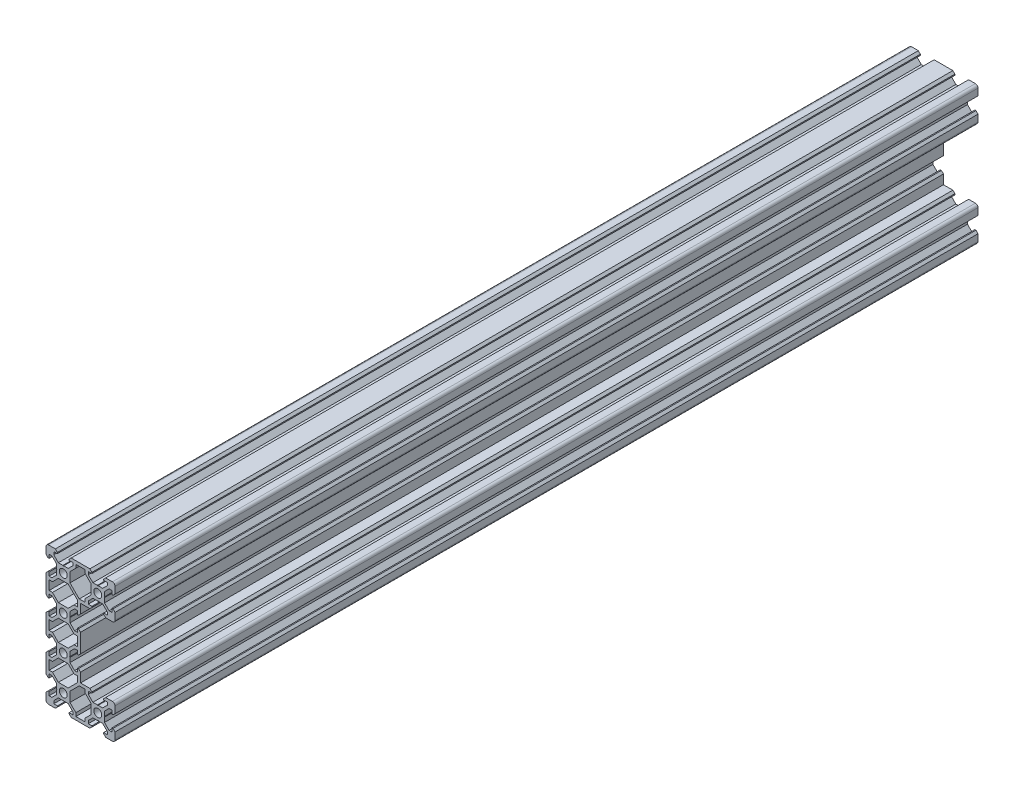
SolidWorks part; units mm, degrees
ref_plane "Front Plane" through (0, 0, 0) normal (0, 0, 1) x (1, 0, 0)
ref_plane "Top Plane" through (0, 0, 0) normal (0, 1, 0) x (1, 0, 0)
ref_plane "Right Plane" through (0, 0, 0) normal (1, 0, 0) x (0, 0, -1)
sketch "Sketch1" plane through (0, 0, 0) normal (0, 0, 1) x (1, 0, 0)
  line B0 (0, -5.42) -> (0, 5.42)
  line B1 (17.3, 38.2) -> (17.3, 36.2393)
  line B2 (17.3, 36.2393) -> (13.9, 32.8393)
  line B3 (13.9, 32.8393) -> (13.9, 27.1607)
  line B4 (19.2607, 21.8) -> (13.9, 27.1607)
  line B5 (22.7, 21.8) -> (19.2607, 21.8)
  line B6 (22.7, 21.8) -> (22.7, 23.7607)
  line B7 (22.7, 23.7607) -> (26.1, 27.1607)
  line B8 (26.1, 32.8393) -> (26.1, 27.1607)
  line B9 (22.7, 36.2393) -> (26.1, 32.8393)
  line B10 (22.7, 38.2) -> (22.7, 36.2393)
  line B11 (17.3, 38.2) -> (22.7, 38.2)
  line B12 (1.8, -22.7) -> (3.7607, -22.7)
  line B13 (3.7607, -22.7) -> (7.1607, -26.1)
  line B14 (7.1607, -26.1) -> (12.8393, -26.1)
  line B15 (18.2, -20.7393) -> (12.8393, -26.1)
  line B16 (18.2, -17.3) -> (18.2, -20.7393)
  line B17 (18.2, -17.3) -> (16.2393, -17.3)
  line B18 (16.2393, -17.3) -> (12.8393, -13.9)
  line B19 (7.1607, -13.9) -> (12.8393, -13.9)
  line B20 (3.7607, -17.3) -> (7.1607, -13.9)
  line B21 (1.8, -17.3) -> (3.7607, -17.3)
  line B22 (1.8, -22.7) -> (1.8, -17.3)
  line B23 (22.7, -38.2) -> (22.7, -36.2393)
  line B24 (22.7, -36.2393) -> (26.1, -32.8393)
  line B25 (26.1, -32.8393) -> (26.1, -27.1607)
  line B26 (22.7, -23.7607) -> (26.1, -27.1607)
  line B27 (22.7, -21.8) -> (22.7, -23.7607)
  line B28 (22.7, -21.8) -> (19.2607, -21.8)
  line B29 (13.9, -27.1607) -> (19.2607, -21.8)
  line B30 (13.9, -32.8393) -> (13.9, -27.1607)
  line B31 (17.3, -36.2393) -> (13.9, -32.8393)
  line B32 (17.3, -38.2) -> (17.3, -36.2393)
  line B33 (22.7, -38.2) -> (17.3, -38.2)
  line B34 (1.8, 17.3) -> (3.7607, 17.3)
  line B35 (3.7607, 17.3) -> (7.1607, 13.9)
  line B36 (7.1607, 13.9) -> (12.8393, 13.9)
  line B37 (16.2393, 17.3) -> (12.8393, 13.9)
  line B38 (18.2, 17.3) -> (16.2393, 17.3)
  line B39 (18.2, 17.3) -> (18.2, 20.7393)
  line B40 (12.8393, 26.1) -> (18.2, 20.7393)
  line B41 (7.1607, 26.1) -> (12.8393, 26.1)
  line B42 (3.7607, 22.7) -> (7.1607, 26.1)
  line B43 (1.8, 22.7) -> (3.7607, 22.7)
  line B44 (1.8, 17.3) -> (1.8, 22.7)
  line B45 (1.8, -2.7) -> (3.7607, -2.7)
  line B46 (3.7607, -2.7) -> (7.1607, -6.1)
  line B47 (7.1607, -6.1) -> (12.8393, -6.1)
  line B48 (16.2393, -2.7) -> (12.8393, -6.1)
  line B49 (18.2, -2.7) -> (16.2393, -2.7)
  line B50 (18.2, -2.7) -> (18.2, 2.7)
  line B51 (18.2, 2.7) -> (16.2393, 2.7)
  line B52 (16.2393, 2.7) -> (12.8393, 6.1)
  line B53 (7.1607, 6.1) -> (12.8393, 6.1)
  line B54 (3.7607, 2.7) -> (7.1607, 6.1)
  line B55 (1.8, 2.7) -> (3.7607, 2.7)
  line B56 (1.8, -2.7) -> (1.8, 2.7)
  line B57 (33.69, 30) -> (33.9, 29.79)
  line B58 (33.9, 29.79) -> (33.9, 27.1607)
  line B59 (33.9, 27.1607) -> (36.5607, 24.5)
  line B60 (36.5607, 24.5) -> (38.2, 24.5)
  line B61 (38.2, 24.5) -> (38.2, 26.605)
  line B62 (38.2, 26.605) -> (38.815, 26.605)
  line B63 (38.815, 26.605) -> (40, 25.42)
  line B64 (40, 25.42) -> (40, 21.5)
  arc B65 (38.5, 20) -> (40, 21.5) centre (38.5, 21.5) ccw
  line B66 (38.5, 20) -> (34.58, 20)
  line B67 (33.395, 21.185) -> (34.58, 20)
  line B68 (33.395, 21.8) -> (33.395, 21.185)
  line B69 (35.5, 21.8) -> (33.395, 21.8)
  line B70 (35.5, 23.4393) -> (35.5, 21.8)
  line B71 (32.8393, 26.1) -> (35.5, 23.4393)
  line B72 (30.21, 26.1) -> (32.8393, 26.1)
  line B73 (30, 26.31) -> (30.21, 26.1)
  line B74 (30, 26.31) -> (29.79, 26.1)
  line B75 (29.79, 26.1) -> (27.1607, 26.1)
  line B76 (27.1607, 26.1) -> (24.5, 23.4393)
  line B77 (24.5, 23.4393) -> (24.5, 21.8)
  line B78 (24.5, 21.8) -> (26.605, 21.8)
  line B79 (26.605, 21.8) -> (26.605, 21.185)
  line B80 (26.605, 21.185) -> (25.42, 20)
  line B81 (25.42, 20) -> (20, 20)
  line B82 (20, 20) -> (20, 14.58)
  line B83 (18.815, 13.395) -> (20, 14.58)
  line B84 (18.2, 13.395) -> (18.815, 13.395)
  line B85 (18.2, 15.5) -> (18.2, 13.395)
  line B86 (16.5607, 15.5) -> (18.2, 15.5)
  line B87 (13.9, 12.8393) -> (16.5607, 15.5)
  line B88 (13.9, 10.21) -> (13.9, 12.8393)
  line B89 (13.69, 10) -> (13.9, 10.21)
  line B90 (13.69, 10) -> (13.9, 9.79)
  line B91 (13.9, 9.79) -> (13.9, 7.1607)
  line B92 (13.9, 7.1607) -> (16.5607, 4.5)
  line B93 (16.5607, 4.5) -> (18.2, 4.5)
  line B94 (18.2, 4.5) -> (18.2, 6.605)
  line B95 (18.2, 6.605) -> (18.815, 6.605)
  line B96 (18.815, 6.605) -> (20, 5.42)
  line B97 (20, 5.42) -> (20, -5.42)
  line B98 (18.815, -6.605) -> (20, -5.42)
  line B99 (18.2, -6.605) -> (18.815, -6.605)
  line B100 (18.2, -4.5) -> (18.2, -6.605)
  line B101 (16.5607, -4.5) -> (18.2, -4.5)
  line B102 (13.9, -7.1607) -> (16.5607, -4.5)
  line B103 (13.9, -9.79) -> (13.9, -7.1607)
  line B104 (13.69, -10) -> (13.9, -9.79)
  line B105 (13.69, -10) -> (13.9, -10.21)
  line B106 (13.9, -10.21) -> (13.9, -12.8393)
  line B107 (13.9, -12.8393) -> (16.5607, -15.5)
  line B108 (16.5607, -15.5) -> (18.2, -15.5)
  line B109 (18.2, -15.5) -> (18.2, -13.395)
  line B110 (18.2, -13.395) -> (18.815, -13.395)
  line B111 (18.815, -13.395) -> (20, -14.58)
  line B112 (20, -14.58) -> (20, -20)
  line B113 (25.42, -20) -> (20, -20)
  line B114 (26.605, -21.185) -> (25.42, -20)
  line B115 (26.605, -21.8) -> (26.605, -21.185)
  line B116 (24.5, -21.8) -> (26.605, -21.8)
  line B117 (24.5, -23.4393) -> (24.5, -21.8)
  line B118 (27.1607, -26.1) -> (24.5, -23.4393)
  line B119 (29.79, -26.1) -> (27.1607, -26.1)
  line B120 (30, -26.31) -> (29.79, -26.1)
  line B121 (30, -26.31) -> (30.21, -26.1)
  line B122 (30.21, -26.1) -> (32.8393, -26.1)
  line B123 (32.8393, -26.1) -> (35.5, -23.4393)
  line B124 (35.5, -23.4393) -> (35.5, -21.8)
  line B125 (35.5, -21.8) -> (33.395, -21.8)
  line B126 (33.395, -21.8) -> (33.395, -21.185)
  line B127 (33.395, -21.185) -> (34.58, -20)
  line B128 (38.5, -20) -> (34.58, -20)
  arc B129 (40, -21.5) -> (38.5, -20) centre (38.5, -21.5) ccw
  line B130 (40, -25.42) -> (40, -21.5)
  line B131 (38.815, -26.605) -> (40, -25.42)
  line B132 (38.2, -26.605) -> (38.815, -26.605)
  line B133 (38.2, -24.5) -> (38.2, -26.605)
  line B134 (36.5607, -24.5) -> (38.2, -24.5)
  line B135 (33.9, -27.1607) -> (36.5607, -24.5)
  line B136 (33.9, -29.79) -> (33.9, -27.1607)
  line B137 (33.69, -30) -> (33.9, -29.79)
  line B138 (33.69, -30) -> (33.9, -30.21)
  line B139 (33.9, -30.21) -> (33.9, -32.8393)
  line B140 (33.9, -32.8393) -> (36.5607, -35.5)
  line B141 (36.5607, -35.5) -> (38.2, -35.5)
  line B142 (38.2, -35.5) -> (38.2, -33.395)
  line B143 (38.2, -33.395) -> (38.815, -33.395)
  line B144 (38.815, -33.395) -> (40, -34.58)
  line B145 (40, -38.5) -> (40, -34.58)
  arc B146 (38.5, -40) -> (40, -38.5) centre (38.5, -38.5) ccw
  line B147 (34.58, -40) -> (38.5, -40)
  line B148 (33.395, -38.815) -> (34.58, -40)
  line B149 (33.395, -38.2) -> (33.395, -38.815)
  line B150 (35.5, -38.2) -> (33.395, -38.2)
  line B151 (35.5, -36.5607) -> (35.5, -38.2)
  line B152 (32.8393, -33.9) -> (35.5, -36.5607)
  line B153 (30.21, -33.9) -> (32.8393, -33.9)
  line B154 (30, -33.69) -> (30.21, -33.9)
  line B155 (30, -33.69) -> (29.79, -33.9)
  line B156 (29.79, -33.9) -> (27.1607, -33.9)
  line B157 (27.1607, -33.9) -> (24.5, -36.5607)
  line B158 (24.5, -36.5607) -> (24.5, -38.2)
  line B159 (24.5, -38.2) -> (26.605, -38.2)
  line B160 (26.605, -38.2) -> (26.605, -38.815)
  line B161 (26.605, -38.815) -> (25.42, -40)
  line B162 (14.58, -40) -> (25.42, -40)
  line B163 (13.395, -38.815) -> (14.58, -40)
  line B164 (13.395, -38.2) -> (13.395, -38.815)
  line B165 (15.5, -38.2) -> (13.395, -38.2)
  line B166 (15.5, -36.5607) -> (15.5, -38.2)
  line B167 (12.8393, -33.9) -> (15.5, -36.5607)
  line B168 (10.21, -33.9) -> (12.8393, -33.9)
  line B169 (10, -33.69) -> (10.21, -33.9)
  line B170 (10, -33.69) -> (9.79, -33.9)
  line B171 (9.79, -33.9) -> (7.1607, -33.9)
  line B172 (7.1607, -33.9) -> (4.5, -36.5607)
  line B173 (4.5, -36.5607) -> (4.5, -38.2)
  line B174 (4.5, -38.2) -> (6.605, -38.2)
  line B175 (6.605, -38.2) -> (6.605, -38.815)
  line B176 (6.605, -38.815) -> (5.42, -40)
  line B177 (1.5, -40) -> (5.42, -40)
  arc B178 (0, -38.5) -> (1.5, -40) centre (1.5, -38.5) ccw
  line B179 (0, -38.5) -> (0, -34.58)
  line B180 (1.185, -33.395) -> (0, -34.58)
  line B181 (1.8, -33.395) -> (1.185, -33.395)
  line B182 (1.8, -35.5) -> (1.8, -33.395)
  line B183 (3.4393, -35.5) -> (1.8, -35.5)
  line B184 (6.1, -32.8393) -> (3.4393, -35.5)
  line B185 (6.1, -30.21) -> (6.1, -32.8393)
  line B186 (6.31, -30) -> (6.1, -30.21)
  line B187 (6.31, -30) -> (6.1, -29.79)
  line B188 (6.1, -29.79) -> (6.1, -27.1607)
  line B189 (6.1, -27.1607) -> (3.4393, -24.5)
  line B190 (3.4393, -24.5) -> (1.8, -24.5)
  line B191 (1.8, -24.5) -> (1.8, -26.605)
  line B192 (1.8, -26.605) -> (1.185, -26.605)
  line B193 (1.185, -26.605) -> (0, -25.42)
  line B194 (0, -25.42) -> (0, -14.58)
  line B195 (1.185, -13.395) -> (0, -14.58)
  line B196 (1.8, -13.395) -> (1.185, -13.395)
  line B197 (1.8, -15.5) -> (1.8, -13.395)
  line B198 (3.4393, -15.5) -> (1.8, -15.5)
  line B199 (6.1, -12.8393) -> (3.4393, -15.5)
  line B200 (6.1, -10.21) -> (6.1, -12.8393)
  line B201 (6.31, -10) -> (6.1, -10.21)
  line B202 (6.31, -10) -> (6.1, -9.79)
  line B203 (6.1, -9.79) -> (6.1, -7.1607)
  line B204 (6.1, -7.1607) -> (3.4393, -4.5)
  line B205 (3.4393, -4.5) -> (1.8, -4.5)
  line B206 (1.8, -4.5) -> (1.8, -6.605)
  line B207 (1.8, -6.605) -> (1.185, -6.605)
  line B208 (1.185, -6.605) -> (0, -5.42)
  line B209 (1.185, 6.605) -> (0, 5.42)
  line B210 (1.8, 6.605) -> (1.185, 6.605)
  line B211 (1.8, 4.5) -> (1.8, 6.605)
  line B212 (3.4393, 4.5) -> (1.8, 4.5)
  line B213 (6.1, 7.1607) -> (3.4393, 4.5)
  line B214 (6.1, 9.79) -> (6.1, 7.1607)
  line B215 (6.31, 10) -> (6.1, 9.79)
  line B216 (6.31, 10) -> (6.1, 10.21)
  line B217 (6.1, 10.21) -> (6.1, 12.8393)
  line B218 (6.1, 12.8393) -> (3.4393, 15.5)
  line B219 (3.4393, 15.5) -> (1.8, 15.5)
  line B220 (1.8, 15.5) -> (1.8, 13.395)
  line B221 (1.8, 13.395) -> (1.185, 13.395)
  line B222 (1.185, 13.395) -> (0, 14.58)
  line B223 (0, 14.58) -> (0, 25.42)
  line B224 (1.185, 26.605) -> (0, 25.42)
  line B225 (1.8, 26.605) -> (1.185, 26.605)
  line B226 (1.8, 24.5) -> (1.8, 26.605)
  line B227 (3.4393, 24.5) -> (1.8, 24.5)
  line B228 (6.1, 27.1607) -> (3.4393, 24.5)
  line B229 (6.1, 29.79) -> (6.1, 27.1607)
  line B230 (6.31, 30) -> (6.1, 29.79)
  line B231 (6.31, 30) -> (6.1, 30.21)
  line B232 (6.1, 30.21) -> (6.1, 32.8393)
  line B233 (6.1, 32.8393) -> (3.4393, 35.5)
  line B234 (3.4393, 35.5) -> (1.8, 35.5)
  line B235 (1.8, 35.5) -> (1.8, 33.395)
  line B236 (1.8, 33.395) -> (1.185, 33.395)
  line B237 (1.185, 33.395) -> (0, 34.58)
  line B238 (0, 34.58) -> (0, 38.5)
  arc B239 (1.5, 40) -> (0, 38.5) centre (1.5, 38.5) ccw
  line B240 (1.5, 40) -> (5.42, 40)
  line B241 (6.605, 38.815) -> (5.42, 40)
  line B242 (6.605, 38.2) -> (6.605, 38.815)
  line B243 (4.5, 38.2) -> (6.605, 38.2)
  line B244 (4.5, 36.5607) -> (4.5, 38.2)
  line B245 (7.1607, 33.9) -> (4.5, 36.5607)
  line B246 (9.79, 33.9) -> (7.1607, 33.9)
  line B247 (10, 33.69) -> (9.79, 33.9)
  line B248 (10, 33.69) -> (10.21, 33.9)
  line B249 (10.21, 33.9) -> (12.8393, 33.9)
  line B250 (12.8393, 33.9) -> (15.5, 36.5607)
  line B251 (15.5, 36.5607) -> (15.5, 38.2)
  line B252 (15.5, 38.2) -> (13.395, 38.2)
  line B253 (13.395, 38.2) -> (13.395, 38.815)
  line B254 (13.395, 38.815) -> (14.58, 40)
  line B255 (14.58, 40) -> (25.42, 40)
  line B256 (26.605, 38.815) -> (25.42, 40)
  line B257 (26.605, 38.2) -> (26.605, 38.815)
  line B258 (24.5, 38.2) -> (26.605, 38.2)
  line B259 (24.5, 36.5607) -> (24.5, 38.2)
  line B260 (27.1607, 33.9) -> (24.5, 36.5607)
  line B261 (29.79, 33.9) -> (27.1607, 33.9)
  line B262 (30, 33.69) -> (29.79, 33.9)
  line B263 (30, 33.69) -> (30.21, 33.9)
  line B264 (30.21, 33.9) -> (32.8393, 33.9)
  line B265 (32.8393, 33.9) -> (35.5, 36.5607)
  line B266 (35.5, 36.5607) -> (35.5, 38.2)
  line B267 (35.5, 38.2) -> (33.395, 38.2)
  line B268 (33.395, 38.2) -> (33.395, 38.815)
  line B269 (33.395, 38.815) -> (34.58, 40)
  line B270 (34.58, 40) -> (38.5, 40)
  arc B271 (40, 38.5) -> (38.5, 40) centre (38.5, 38.5) ccw
  line B272 (40, 38.5) -> (40, 34.58)
  line B273 (38.815, 33.395) -> (40, 34.58)
  line B274 (38.2, 33.395) -> (38.815, 33.395)
  line B275 (38.2, 35.5) -> (38.2, 33.395)
  line B276 (36.5607, 35.5) -> (38.2, 35.5)
  line B277 (33.9, 32.8393) -> (36.5607, 35.5)
  line B278 (33.9, 30.21) -> (33.9, 32.8393)
  line B279 (33.69, 30) -> (33.9, 30.21)
  circle B280 centre (30, -30) radius 2.3
  circle B281 centre (30, 30) radius 2.3
  circle B282 centre (10, 30) radius 2.3
  circle B283 centre (10, 10) radius 2.3
  circle B284 centre (10, -10) radius 2.3
  circle B285 centre (10, -30) radius 2.3
sketch_block_instance "C-Beam 4080 - V-Slot-1"
sketch_block "C-Beam 4080 - V-Slot"
extrude "Boss-Extrude1" add sketch "Sketch1" along normal blind 500
